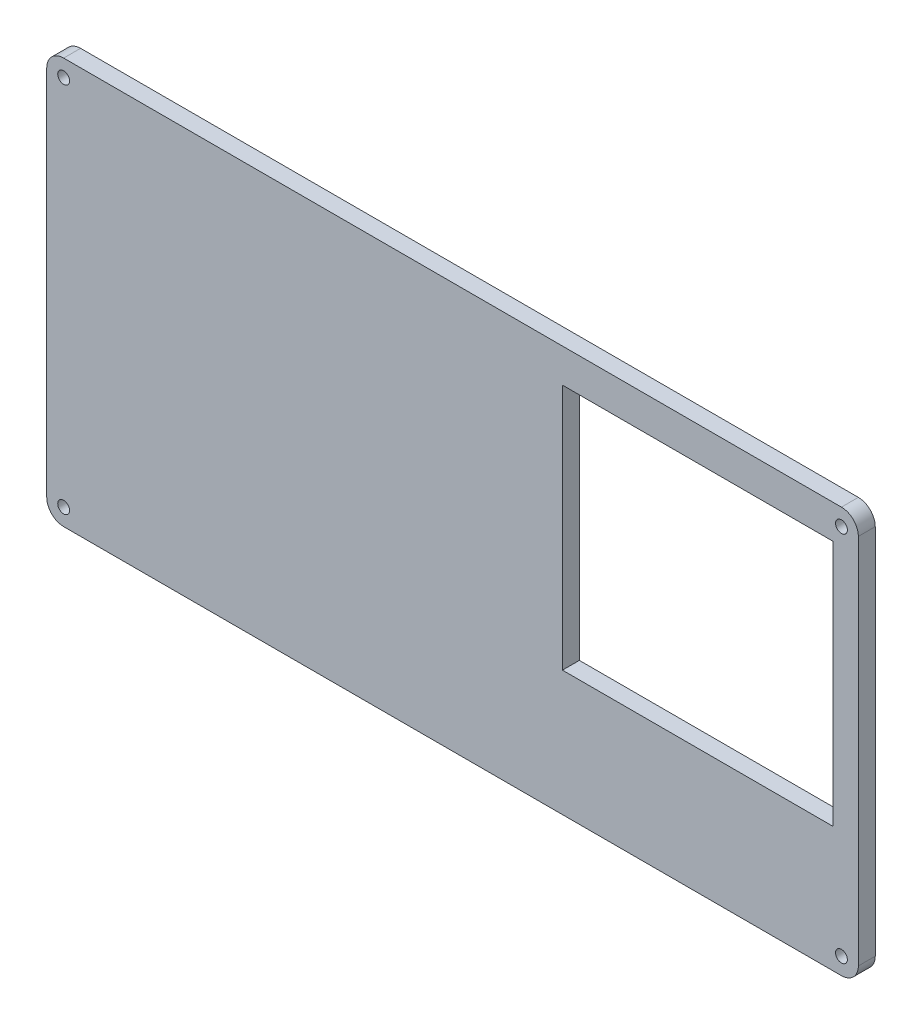
SolidWorks part; units mm, degrees
ref_plane "Front Plane" through (0, 0, 0) normal (0, 0, 1) x (1, 0, 0)
ref_plane "Top Plane" through (0, 0, 0) normal (0, 1, 0) x (1, 0, 0)
ref_plane "Right Plane" through (0, 0, 0) normal (1, 0, 0) x (0, 0, -1)
sketch "Sketch1" plane through (0, 0, 0) normal (0, 0, 1) x (1, 0, 0)
  line L0 (-115, -60) -> (115, -60)
  line L5 (-120, 55) -> (-120, -55)
  line L6 (0, 60) -> (0, -60) construction
  line L7 (-115, 60) -> (115, 60)
  line L8 (120, 55) -> (120, -55)
  arc A4 (-115, 60) -> (-120, 55) centre (-115, 55) ccw
  arc A5 (-120, -55) -> (-115, -60) centre (-115, -55) ccw
  arc A6 (120, -55) -> (115, -60) centre (115, -55) cw
  arc A7 (115, 60) -> (120, 55) centre (115, 55) cw
  point P0 (0, 0)
  point P22 (0, -60)
  point P27 (0, 60)
  dimension "D1" = 240
  dimension "D3" = 5
  dimension "D4" = 5
  dimension "D2" = 110
extrude "Boss-Extrude1" add sketch "Sketch1" along normal blind 5
sketch "Sketch2" plane through (0, 0, 5) normal (0, 0, 1) x (1, 0, 0)
  line L0 (0, 70.8296) -> (0, -79.1128) construction
  line L1 (-140.7295, 0) -> (155.0983, 0) construction
  circle A0 centre (-115, 55) radius 1.75
  arc A1 (-115, 60) -> (-120, 55) centre (-115, 55) ccw construction
  circle A2 centre (115, 55) radius 1.75
  circle A3 centre (115, -55) radius 1.75
  circle A4 centre (-115, -55) radius 1.75
  dimension "D1" = 3.5
extrude "lukne_m3_vijaki" cut sketch "Sketch2" against normal blind 5
sketch "Sketch3" plane through (0, 0, 5) normal (0, 0, 1) x (1, 0, 0)
  line L0 (120, -55) -> (120, 55) construction
  line L1 (32.5, 50) -> (112.5, 50)
  line L2 (32.5, 50) -> (32.5, -23)
  line L3 (32.5, -23) -> (112.5, -23)
  line L4 (112.5, 50) -> (112.5, -23)
  line L5 (115, 60) -> (-115, 60) construction
  dimension "D1" = 7.5
  dimension "D2" = 10
  dimension "D3" = 80
  dimension "D4" = 73
extrude "Cut-Extrude2" cut sketch "Sketch3" against normal blind 5
